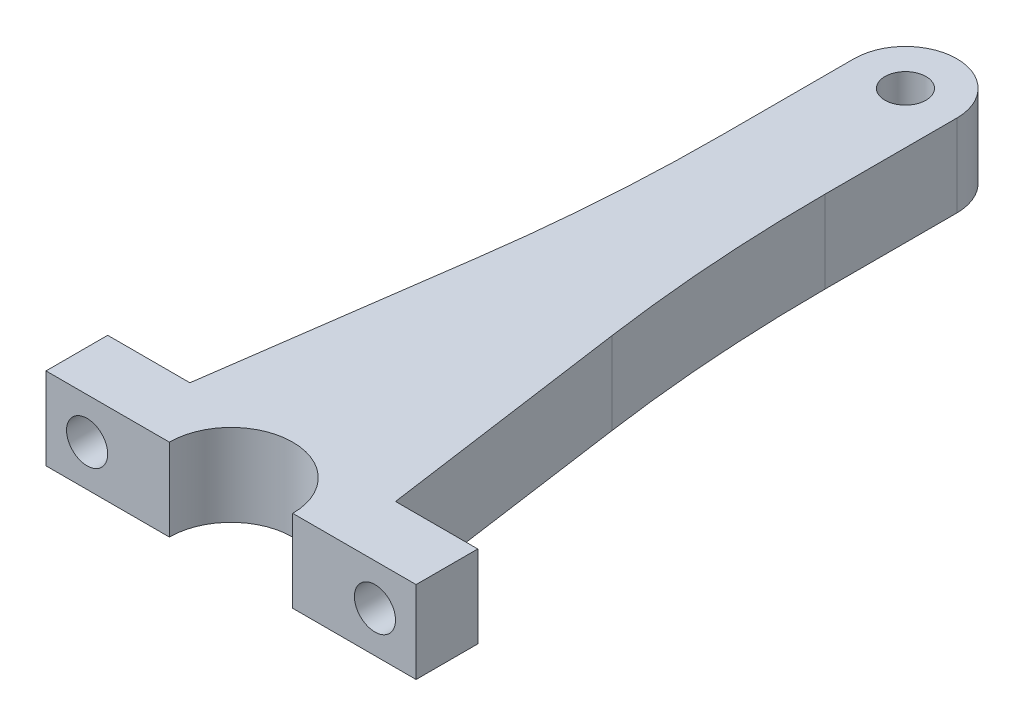
SolidWorks part; units mm, degrees
ref_plane "Front Plane" through (0, 0, 0) normal (0, 0, 1) x (1, 0, 0)
ref_plane "Top Plane" through (0, 0, 0) normal (0, 1, 0) x (1, 0, 0)
ref_plane "Right Plane" through (0, 0, 0) normal (1, 0, 0) x (0, 0, -1)
sketch "Sketch1" plane through (0, 0, 0) normal (0, 1, 0) x (1, 0, 0)
  line L0 (0, 0) -> (0, 96.4421) construction
  line L1 (-25, 7.5) -> (-12.5, 96.4421)
  line L2 (-45, -7.5) -> (45, -7.5)
  line L3 (-45, -7.5) -> (-45, 7.5)
  line L4 (-45, 7.5) -> (45, 7.5)
  line L5 (45, -7.5) -> (45, 7.5)
  line L6 (-45, -7.5) -> (45, 7.5) construction
  line L7 (-45, 7.5) -> (45, -7.5) construction
  line L8 (25, 7.5) -> (12.5, 96.4421)
  line L10 (-12.5, 96.4421) -> (12.5, 96.4421)
  line L11 (-12.5, 96.4421) -> (-12.5, 156.5)
  line L12 (-12.5, 156.5) -> (12.5, 156.5)
  line L13 (12.5, 96.4421) -> (12.5, 156.5)
  circle A0 centre (0, 156.5) radius 12.5
  circle A1 centre (0, 156.5) radius 5
  circle A2 centre (0, -7.5) radius 15
  dimension "D5" = 10
  dimension "D6" = 149
  dimension "D8" = 30
  dimension "D1" = 15
  dimension "D2" = 90
  dimension "D3" = 16
  dimension "D4" = 25
  dimension "D7" = 20
extrude "Boss-Extrude1" add sketch "Sketch1" along normal blind 20 contours A1 L12 A0 | A1 L12 A0 | A0 L11 L10 L13 | L10 L1 L4 L8 | A2 L4 L3 L2 | A2 L2 L5 L4
sketch "Sketch2" plane through (0, 0, -7.5) normal (0, 0, -1) x (-1, 0, 0)
  line L0 (-45, 10) -> (45, 10) construction
  line L1 (-45, 20) -> (-45, 0) construction
  line L2 (45, 20) -> (45, 0) construction
  line L3 (0, 0) -> (0, -10.3393) construction
  circle A0 centre (35, 10) radius 5
  circle A1 centre (-35, 10) radius 5
  dimension "D1" = 10
  dimension "D2" = 70
extrude "Cut-Extrude1" cut sketch "Sketch2" against normal through all
fillet "Fillet1" radius 400 2 edges at (-12.5, 10, -96.4421) (12.5, 10, -96.4421)
